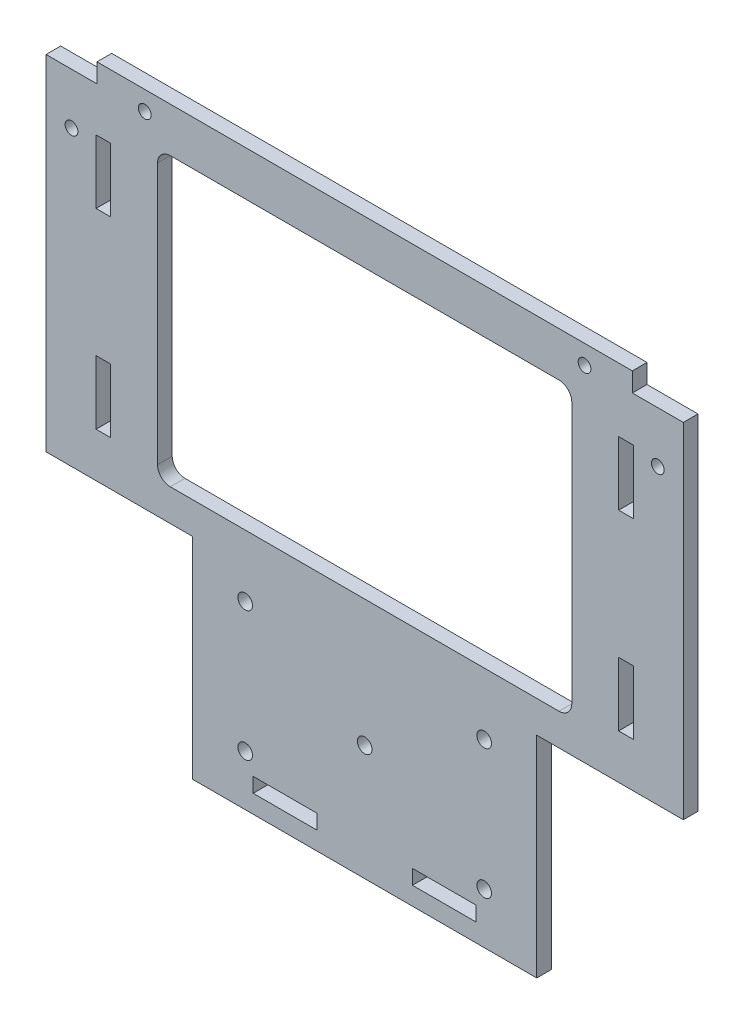
SolidWorks part; units mm, degrees
ref_plane "Front Plane" through (0, 0, 0) normal (0, 0, 1) x (1, 0, 0)
ref_plane "Top Plane" through (0, 0, 0) normal (0, 1, 0) x (1, 0, 0)
ref_plane "Right Plane" through (0, 0, 0) normal (1, 0, 0) x (0, 0, -1)
sketch "Sketch1" plane through (0, 0, 0) normal (0, 0, 1) x (1, 0, 0)
  line L1 (0, 0) -> (100, 0)
  line L2 (0, 0) -> (0, -57)
  line L4 (100, 0) -> (100, -57)
  line L7 (0, -57) -> (23, -57)
  line L8 (23, -90) -> (23, -57)
  line L11 (100, -57) -> (77, -57)
  line L12 (77, -90) -> (77, -57)
  line L14 (23, -90) -> (77, -90)
  dimension "D1" = 100
  dimension "D2" = 57
  dimension "D3" = 23
  dimension "D4" = 23
  dimension "D5" = 33
  dimension "D6" = 33
  dimension "D7" = 54
extrude "Boss-Extrude1" add sketch "Sketch1" along normal blind 2.3
sketch "Sketch5" plane through (0, 0, 2.3) normal (0, 0, 1) x (1, 0, 0)
  line L0 (50, 0) -> (50, -90) construction
  line L1 (100, 0) -> (0, 0) construction
  line L2 (23, -90) -> (77, -90) construction
  line L3 (0, -57) -> (23, -57) construction
  line L4 (17.5, -52) -> (82.5, -52)
  line L5 (17.5, -52) -> (17.5, -7)
  line L6 (17.5, -7) -> (82.5, -7)
  line L7 (82.5, -52) -> (82.5, -7)
  line L8 (17.5, -52) -> (82.5, -7) construction
  line L9 (17.5, -7) -> (82.5, -52) construction
  point P6 (50, -29.5)
  dimension "D1" = 65
  dimension "D2" = 45
  dimension "D3" = 5
extrude "Cut-Extrude1" cut sketch "Sketch5" against normal through all
fillet "Fillet1" radius 2 4 edges at (82.5, -52, 1.15) (82.5, -7, 1.15) (17.5, -7, 1.15) (17.5, -52, 1.15)
sketch "Sketch7" plane through (0, 0, 2.3) normal (0, 0, 1) x (1, 0, 0)
  line L0 (100, -57) -> (100, 0) construction
  line L3 (89.85, -10) -> (92.15, -10)
  line L4 (89.85, -10) -> (89.85, -20)
  line L5 (89.85, -20) -> (92.15, -20)
  line L6 (92.15, -10) -> (92.15, -20)
  line L7 (89.85, -10) -> (92.15, -20) construction
  line L8 (89.85, -20) -> (92.15, -10) construction
  line L9 (100, 0) -> (0, 0) construction
  line L10 (89.85, -40) -> (92.15, -50) construction
  line L11 (92.15, -40) -> (92.15, -50)
  line L12 (89.85, -40) -> (89.85, -50)
  line L13 (89.85, -50) -> (92.15, -40) construction
  line L14 (89.85, -40) -> (92.15, -40)
  line L15 (89.85, -50) -> (92.15, -50)
  line L16 (7.85, -10) -> (10.15, -10)
  line L17 (7.85, -20) -> (10.15, -10) construction
  line L18 (7.85, -10) -> (7.85, -20)
  line L19 (7.85, -20) -> (10.15, -20)
  line L20 (10.15, -10) -> (10.15, -20)
  line L21 (7.85, -10) -> (10.15, -20) construction
  line L22 (0, 0) -> (0, -57) construction
  line L23 (7.85, -50) -> (10.15, -40) construction
  line L24 (10.15, -40) -> (10.15, -50)
  line L25 (7.85, -50) -> (10.15, -50)
  line L26 (7.85, -40) -> (10.15, -50) construction
  line L27 (7.85, -40) -> (7.85, -50)
  line L28 (7.85, -40) -> (10.15, -40)
  line L29 (23, -90) -> (77, -90) construction
  line L30 (32.5, -87.15) -> (42.5, -87.15)
  line L31 (32.5, -87.15) -> (32.5, -84.85)
  line L32 (32.5, -84.85) -> (42.5, -84.85)
  line L33 (42.5, -87.15) -> (42.5, -84.85)
  line L34 (32.5, -87.15) -> (42.5, -84.85) construction
  line L35 (32.5, -84.85) -> (42.5, -87.15) construction
  line L36 (67.5, -87.15) -> (57.5, -87.15)
  line L37 (67.5, -87.15) -> (67.5, -84.85)
  line L38 (67.5, -84.85) -> (57.5, -84.85)
  line L39 (57.5, -87.15) -> (57.5, -84.85)
  line L40 (67.5, -87.15) -> (57.5, -84.85) construction
  line L41 (67.5, -84.85) -> (57.5, -87.15) construction
  line L42 (77, -90) -> (77, -57) construction
  point P0 (91, -15)
  point P7 (9, -15)
  point P11 (91, -45)
  point P21 (9, -45)
  point P26 (37.5, -86)
  point P31 (62.5, -86)
  dimension "D1" = 2.3
  dimension "D2" = 10
  dimension "D3" = 9
  dimension "D4" = 10
  dimension "D5" = 10
  dimension "D6" = 9
  dimension "D7" = 20
  dimension "D8" = 10
  dimension "D9" = 9
  dimension "D10" = 10
  dimension "D11" = 9
  dimension "D12" = 20
  dimension "D13" = 2.3
  dimension "D14" = 2.3
  dimension "D15" = 10
  dimension "D16" = 2.3
  dimension "D17" = 4
  dimension "D18" = 4
  dimension "D19" = 10
  dimension "D20" = 10
  dimension "D21" = 2.3
  dimension "D22" = 2.3
  dimension "D23" = 15
  dimension "D24" = 9.5
extrude "Cut-Extrude2" cut sketch "Sketch7" against normal through all
sketch "Sketch8" plane through (0, 0, 2.3) normal (0, 0, 1) x (1, 0, 0)
  line L0 (100, 0) -> (0, 0) construction
  line L1 (0, 0) -> (0, -57) construction
  line L2 (100, -57) -> (100, 0) construction
  circle A1 centre (15.5, -3) radius 1
  circle A3 centre (84.5, -3) radius 1
  dimension "D4" = 15.5
  dimension "D5" = 2
  dimension "D10" = 15.5
  dimension "D12" = 2
  dimension "D6" = 3
  dimension "D11" = 3
extrude "Cut-Extrude3" cut sketch "Sketch8" against normal through all
sketch "Sketch10" plane through (0, 0, 2.3) normal (0, 0, 1) x (1, 0, 0)
  line L0 (42.5, -84.85) -> (32.5, -84.85) construction
  line L1 (0, 0) -> (0, -57) construction
  line L3 (24.9997, -61.7) -> (74.9997, -61.7) construction
  line L4 (24.9997, -82.05) -> (74.9997, -82.05) construction
  line L5 (23, -57) -> (23, -90) construction
  line L8 (23, -90) -> (77, -90) construction
  circle A0 centre (49.9997, -71.875) radius 1.15
  circle A1 centre (31.2497, -61.7) radius 1.15
  circle A2 centre (68.7497, -61.7) radius 1.15
  circle A3 centre (31.2497, -82.05) radius 1.15
  circle A4 centre (68.7497, -82.05) radius 1.15
  point P0 (37.5, -84.85)
  point P5 (50, -90)
  dimension "D7" = 2.3
  dimension "D8" = 2.3
  dimension "D9" = 2.3
  dimension "D10" = 2.3
  dimension "D1" = 20.35
  dimension "D2" = 21.3329
  dimension "D3" = 37.5
  dimension "D4" = 2.8
  dimension "D5" = 8.2497
  dimension "D6" = 18.125
  dimension "D11" = 24.9997
  dimension "D12" = 74.9997
extrude "Cut-Extrude4" cut sketch "Sketch10" against normal through all
sketch "Sketch11" plane through (0, 0, 2.3) normal (0, 0, 1) x (1, 0, 0)
  line L0 (0, 0) -> (0, -3)
  line L1 (0, 0) -> (0, -57) construction
  line L2 (0, 0) -> (8, 0)
  line L3 (100, 0) -> (0, 0) construction
  line L4 (0, -3) -> (8, -3)
  line L5 (8, -3) -> (8, 0)
  line L6 (100, 0) -> (92, 0)
  line L7 (100, 0) -> (100, -3)
  line L8 (100, -57) -> (100, 0) construction
  line L9 (100, -3) -> (92, -3)
  line L10 (92, -3) -> (92, 0)
  dimension "D1" = 3
  dimension "D2" = 8
  dimension "D3" = 8
  dimension "D4" = 3
extrude "Cut-Extrude5" cut sketch "Sketch11" against normal blind 10
sketch "Sketch12" plane through (0, 0, 2.3) normal (0, 0, 1) x (1, 0, 0)
  line L0 (4, -3) -> (4, -11) construction
  line L1 (0, -3) -> (8, -3) construction
  line L2 (96, -3) -> (96, -11) construction
  line L3 (92, -3) -> (100, -3) construction
  circle A0 centre (4, -11) radius 1
  circle A1 centre (96, -11) radius 1
  dimension "D3" = 2
  dimension "D1" = 8
  dimension "D2" = 8
extrude "Cut-Extrude6" cut sketch "Sketch12" against normal blind 10
